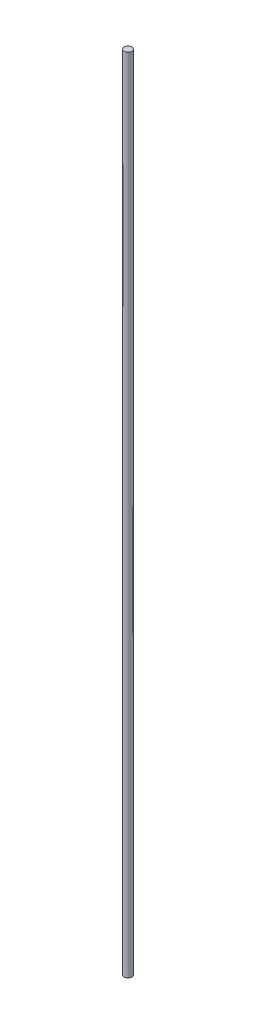
SolidWorks part; units mm, degrees
ref_plane "Front Plane" through (0, 0, 0) normal (0, 0, 1) x (1, 0, 0)
ref_plane "Top Plane" through (0, 0, 0) normal (0, 1, 0) x (1, 0, 0)
ref_plane "Right Plane" through (0, 0, 0) normal (1, 0, 0) x (0, 0, -1)
sketch "Sketch2" plane through (0, 0, 0) normal (0, 0, 1) x (1, 0, 0)
  line L1 (2.3813, 0) -> (2.3813, 500)
  line L2 (0, 1.5875) -> (0, 500)
  line L3 (0, 500) -> (2.3813, 500)
  line L4 (2.3813, 0) -> (0.7937, 0)
  line L5 (0.7937, 0) -> (0.7937, 1.5875)
  line L6 (0.7937, 1.5875) -> (0, 1.5875)
  point P2 (0, 0)
  point P6 (0, 0)
  point P7 (0, 0)
  dimension "D1" = 0.7937
  dimension "D2" = 500
  dimension "D3" = 1.5875
  dimension "D4" = 2.3813
revolve "Revolve1" add sketch "Sketch2" angle 360 about L2
